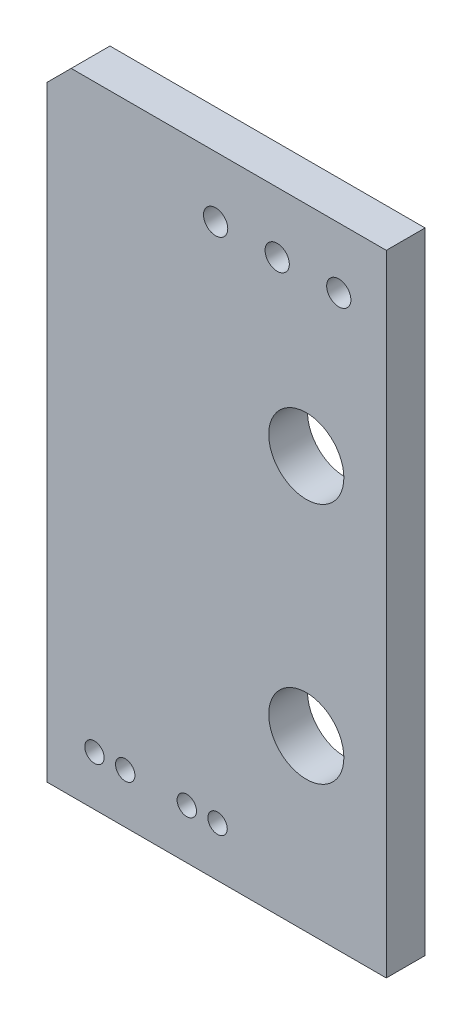
SolidWorks part; units mm, degrees
ref_plane "Front Plane" through (0, 0, 0) normal (0, 0, 1) x (1, 0, 0)
ref_plane "Top Plane" through (0, 0, 0) normal (0, 1, 0) x (1, 0, 0)
ref_plane "Right Plane" through (0, 0, 0) normal (1, 0, 0) x (0, 0, -1)
sketch "Sketch1" plane through (0, 0, 0) normal (0, 0, 1) x (1, 0, 0)
  line L1 (-7, 26) -> (7, 26)
  line L2 (-7, 26) -> (-7, 0)
  line L3 (-7, 0) -> (7, 0)
  line L4 (7, 26) -> (7, 0)
  line L5 (-7, 26) -> (7, 0) construction
  line L6 (-7, 0) -> (7, 26) construction
  line L7 (-6, 2.5) -> (1, 2.5) construction
  line L8 (-6, 2.5) -> (-6, 0) construction
  line L9 (2.5, 23.5) -> (5.04, 23.5) construction
  line L10 (1, 2.5) -> (1, 0) construction
  line L11 (-6, 2.5) -> (1, 0) construction
  line L12 (-6, 0) -> (1, 2.5) construction
  line L14 (2.5, 23.5) -> (-0.04, 23.5) construction
  line L15 (-2.5, 1.25) -> (-2.5, 2.05) construction
  line L16 (-3.77, 2.05) -> (-1.23, 2.05) construction
  line L17 (-1.23, 2.05) -> (0.04, 2.05) construction
  line L18 (-3.77, 2.05) -> (-5.04, 2.05) construction
  circle A0 centre (-0.04, 23.5) radius 0.5
  circle A1 centre (2.5, 23.5) radius 0.5
  circle A2 centre (5.04, 23.5) radius 0.5
  circle A4 centre (-5.04, 2.05) radius 0.4
  circle A5 centre (-3.77, 2.05) radius 0.4
  circle A6 centre (-1.23, 2.05) radius 0.4
  circle A7 centre (0.04, 2.05) radius 0.4
  circle A8 centre (3.7, 7) radius 1.55
  circle A9 centre (3.7, 17) radius 1.55
  point P0 (0, 13)
  point P5 (-2.5, 1.25)
  point P10 (-2, 32.5)
  dimension "D5" = 1
  dimension "D9" = 0.8
  dimension "D15" = 9.5
  dimension "D17" = 3.1
  dimension "D1" = 2.5
  dimension "D2" = 7
  dimension "D3" = 26
  dimension "D4" = 14
  dimension "D6" = 2.54
  dimension "D7" = 5.08
  dimension "D8" = 1.27
  dimension "D10" = 2.05
  dimension "D11" = 8
  dimension "D12" = 7
  dimension "D13" = 10
  dimension "D14" = 10.7
  dimension "D16" = 23.5
extrude "Boss-Extrude1" add sketch "Sketch1" along normal blind 1.6
chamfer "Chamfer1" distance 1 angle 45 1 edges at (-7, 26, 0.8)
